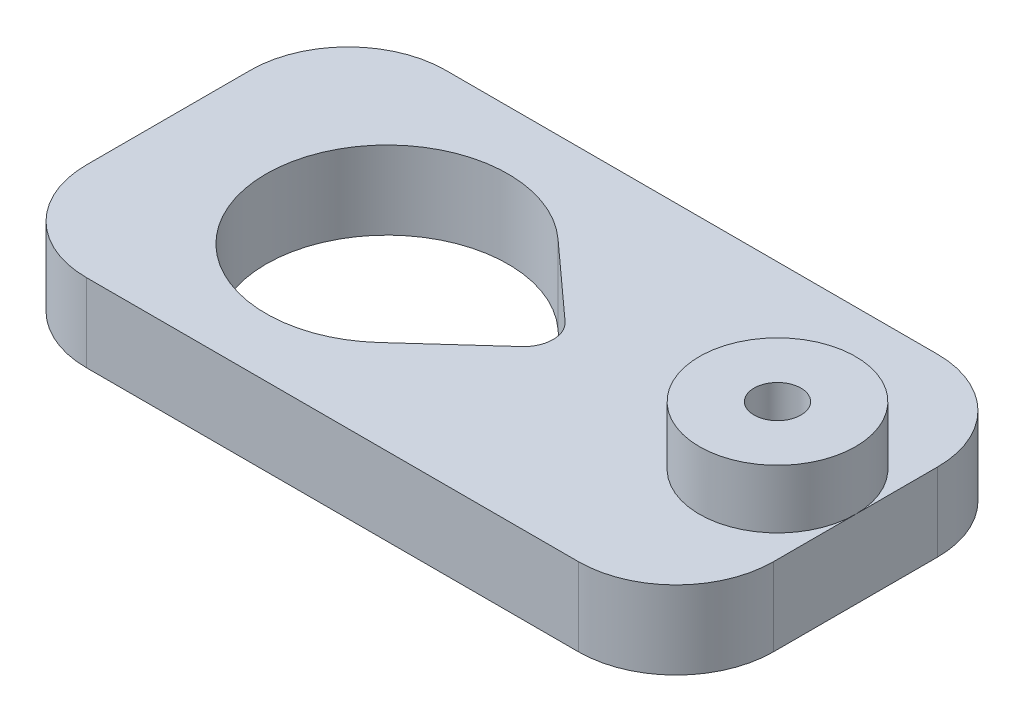
SolidWorks part; units mm, degrees
ref_plane "Спереди" through (0, 0, 0) normal (0, 0, 1) x (1, 0, 0)
ref_plane "Сверху" through (0, 0, 0) normal (0, 1, 0) x (1, 0, 0)
ref_plane "Справа" through (0, 0, 0) normal (1, 0, 0) x (0, 0, -1)
sketch "Эскиз1" plane through (0, 0, 0) normal (0, 1, 0) x (1, 0, 0)
  line L0 (-6.2, 0) -> (16.4, 0) construction
  line L1 (-6.2, 6.2) -> (16.4, 6.2)
  line L2 (-6.2, 6.2) -> (-6.2, -6.2)
  line L3 (-6.2, -6.2) -> (16.4, -6.2)
  line L4 (16.4, 6.2) -> (16.4, -6.2)
  line L5 (5.1, 6.2) -> (5.1, -6.2) construction
  line L6 (-11.2, 6.2) -> (21.4, 6.2)
  line L7 (-11.2, 6.2) -> (-11.2, -6.2)
  line L8 (-11.2, -6.2) -> (21.4, -6.2)
  line L9 (21.4, 6.2) -> (21.4, -6.2)
  line L10 (8.0071, 1.1116) -> (4.1629, 4.5946)
  line L11 (-11.2, 9.2) -> (24, 9.2)
  line L12 (-11.2, 9.2) -> (-11.2, -9.2)
  line L13 (-11.2, -9.2) -> (24, -9.2)
  line L14 (24, 9.2) -> (24, -9.2)
  line L15 (8.0071, -1.1116) -> (4.1629, -4.5946)
  circle A0 centre (0, 0) radius 6.2
  circle A1 centre (20, 0) radius 1.2
  circle A2 centre (7, 0) radius 1.5
  dimension "D3" = 12.4
  dimension "D6" = 2.4
  dimension "D9" = 3
  dimension "D1" = 22.6
  dimension "D2" = 12.4
  dimension "D4" = 32.6
  dimension "D5" = 20
  dimension "D7" = 3
  dimension "D8" = 4
  dimension "D10" = 7
extrude "Бобышка-Вытянуть1" add sketch "Эскиз1" along normal blind 4 contours L14 L11 L12 L6 L1 L9 L8 L3 L13 | L7 L8 L2 L6 | L9 L6 L4 L8 A1 | A2 L15 A0 L8 L4 L6 L10 | A0 L1 L2 | A0 L2 L3
sketch "Эскиз2" plane through (0, 4, 0) normal (0, 1, 0) x (1, 0, 0)
  line L0 (24, 9.2) -> (24, -9.2) construction
  circle A0 centre (20, 0) radius 1.2 construction
  circle A1 centre (20, 0) radius 1.2
  circle A2 centre (20, 0) radius 4
extrude "Бобышка-Вытянуть2" add sketch "Эскиз2" along normal blind 3
fillet "Скругление1" radius 5 4 edges at (24, 2, -9.2) (-11.2, 2, 9.2) (-11.2, 2, -9.2) (24, 2, 9.2)
